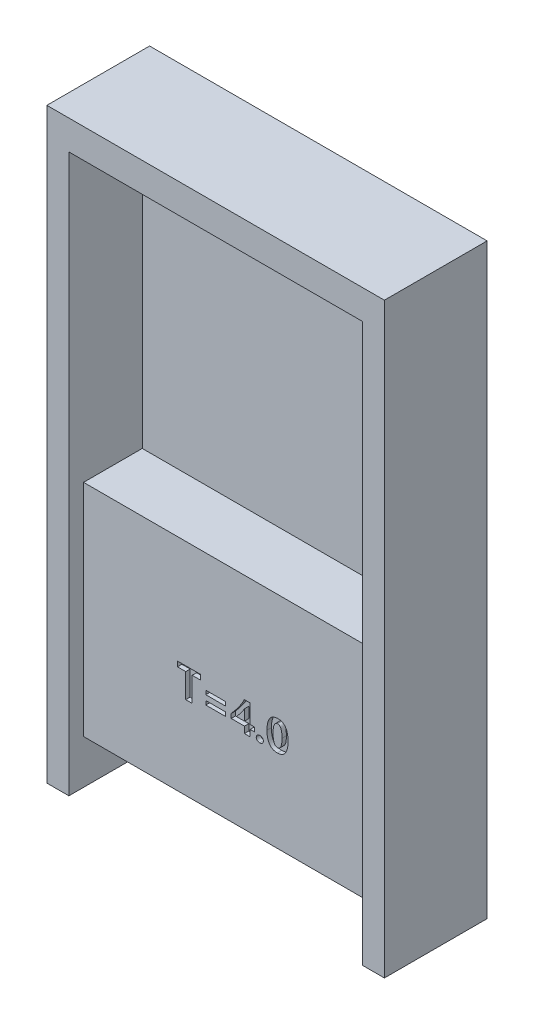
SolidWorks part; units mm, degrees
ref_plane "前视基准面" through (0, 0, 0) normal (0, 0, 1) x (1, 0, 0)
ref_plane "上视基准面" through (0, 0, 0) normal (0, 1, 0) x (1, 0, 0)
ref_plane "右视基准面" through (0, 0, 0) normal (1, 0, 0) x (0, 0, -1)
sketch "草图1" plane through (0, 0, 0) normal (0, 0, 1) x (1, 0, 0)
  line L0 (-1020, 0) -> (-11.5, 0) construction
  line L1 (0, 0) -> (0, 25.9672) construction
  line L2 (-10, 0) -> (-10, -18)
  line L4 (-10, 0) -> (-10, 20)
  line L5 (-10, 20) -> (10, 20)
  line L6 (10, 0) -> (10, 20)
  line L8 (10, -18) -> (10, 0)
  line L10 (-11.5, 22) -> (11.5, 22)
  line L11 (-11.5, 22) -> (-11.5, -18)
  line L12 (-11.5, -18) -> (-10, -18)
  line L13 (11.5, 22) -> (11.5, -18)
  line L15 (10, -18) -> (11.5, -18)
  line L16 (11.5, 0) -> (1020.3279, 0) construction
  point P2 (0, 20)
  point P16 (0, 22)
  point P21 (0, 0)
  point P22 (0, 0)
  point P23 (0, 0)
  point P24 (0, 0)
  dimension "D1" = 20
  dimension "D2" = 20
  dimension "D4" = 23
  dimension "D5" = 40
  dimension "D6" = 22
extrude "凸台-拉伸1" add sketch "草图1" along normal blind 7
sketch "草图2" plane through (0, 0, 0) normal (0, 0, 1) x (1, 0, 0)
  line L0 (0, 0) -> (32.0423, 0) construction
  line L1 (10, 20) -> (10, -18) construction
  line L2 (0, 0) -> (0, 18.5674) construction
  line L3 (-10, 20) -> (10, 20)
  line L4 (-10, 20) -> (-10, -15)
  line L5 (-10, -15) -> (10, -15)
  line L6 (10, 20) -> (10, -15)
  dimension "D1" = 35
extrude "凸台-拉伸2" add sketch "草图2" along normal blind 6
sketch "草图3" plane through (0, 0, 6) normal (0, 0, 1) x (1, 0, 0)
  line L0 (-10, 0) -> (10, 0)
  line L1 (-10, 20) -> (-10, -15) construction
  line L2 (10, -15) -> (10, 20) construction
  line L3 (-10, 0) -> (-10, 20)
  line L4 (-10, 20) -> (10, 20)
  line L5 (10, 20) -> (10, 0)
extrude "切除-拉伸1" cut sketch "草图3" against normal blind 4
sketch "草图4" plane through (0, 0, 0) normal (0, 0, -1) x (-1, 0, 0)
  line L0 (0, 0) -> (0, 18.3654) construction
  line L1 (-7, -2) -> (7, -2)
  line L2 (-7, -2) -> (-7, -12)
  line L3 (-7, -12) -> (7, -12)
  line L4 (7, -2) -> (7, -12)
  line L5 (10, -15) -> (-10, -15) construction
  line L6 (10, 0) -> (-10, 0) construction
  point P5 (0, -2)
  dimension "D1" = 2
  dimension "D2" = 14
  dimension "D3" = 3
extrude "切除-拉伸2" cut sketch "草图4" against normal blind 5
sketch "草图5" plane through (0, 0, 6) normal (0, 0, 1) x (1, 0, 0)
  text T0 "T=4.0" font "微软雅黑" height 2
extrude "切除-拉伸3" cut sketch "草图5" against normal blind 0.3
